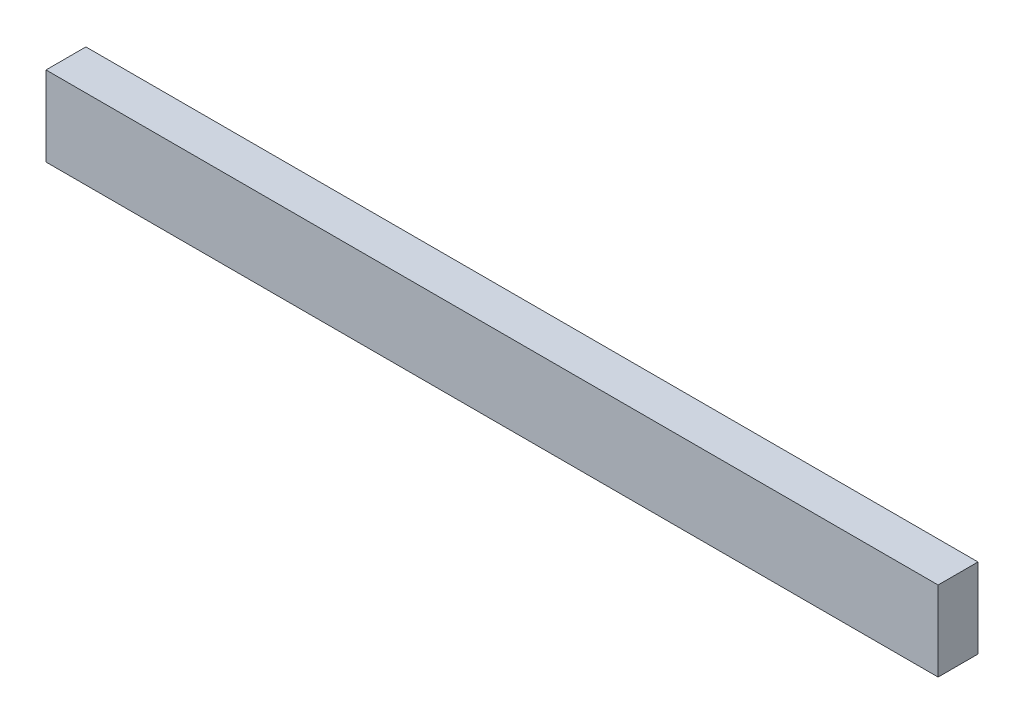
SolidWorks part; units mm, degrees
ref_plane "Front Plane" through (0, 0, 0) normal (0, 0, 1) x (1, 0, 0)
ref_plane "Top Plane" through (0, 0, 0) normal (0, 1, 0) x (1, 0, 0)
ref_plane "Right Plane" through (0, 0, 0) normal (1, 0, 0) x (0, 0, -1)
sketch "Sketch1" plane through (0, 0, 0) normal (1, 0, 0) x (0, 0, -1)
  line L1 (-12.7, -25.4) -> (12.7, -25.4)
  line L2 (-12.7, -25.4) -> (-12.7, 25.4)
  line L3 (-12.7, 25.4) -> (12.7, 25.4)
  line L4 (12.7, -25.4) -> (12.7, 25.4)
  line L5 (-12.7, -25.4) -> (12.7, 25.4) construction
  line L6 (-12.7, 25.4) -> (12.7, -25.4) construction
  point P0 (0, 0)
extrude "Boss-Extrude1" add sketch "Sketch1" along normal blind 568
